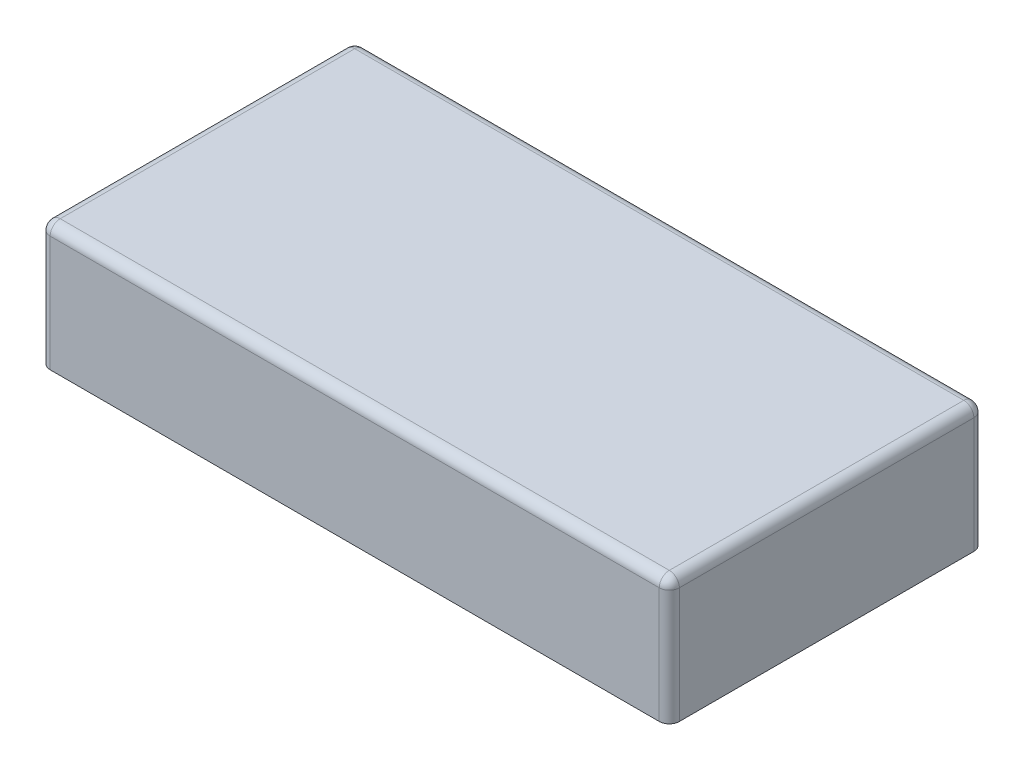
SolidWorks part; units mm, degrees
ref_plane "Front Plane" through (0, 0, 0) normal (0, 0, 1) x (1, 0, 0)
ref_plane "Top Plane" through (0, 0, 0) normal (0, 1, 0) x (1, 0, 0)
ref_plane "Right Plane" through (0, 0, 0) normal (1, 0, 0) x (0, 0, -1)
sketch "Sketch2" plane through (0, 0, 0) normal (0, 1, 0) x (1, 0, 0)
  line L0 (-17.7331, 8.7234) -> (-1.8581, 8.7234)
  line L1 (-1.8581, 8.7234) -> (-1.8581, 0.7859)
  line L2 (-1.8581, 0.7859) -> (-17.7331, 0.7859)
  line L3 (-17.7331, 0.7859) -> (-17.7331, 8.7234)
  dimension "D1" = 15.875
  dimension "D2" = 7.9375
extrude "Boss-Extrude3" add sketch "Sketch2" along normal blind 3.175
shell "Shell1" thickness 1.524
fillet "Fillet1" radius 0.254 8 edges at (-17.7331, 1.5875, -8.7234) (-1.8581, 3.175, -4.7546) (-1.8581, 1.5875, -8.7234) (-1.8581, 1.5875, -0.7859) (-9.7956, 3.175, -0.7859) (-17.7331, 1.5875, -0.7859) (-17.7331, 3.175, -4.7546) (-9.7956, 3.175, -8.7234)
